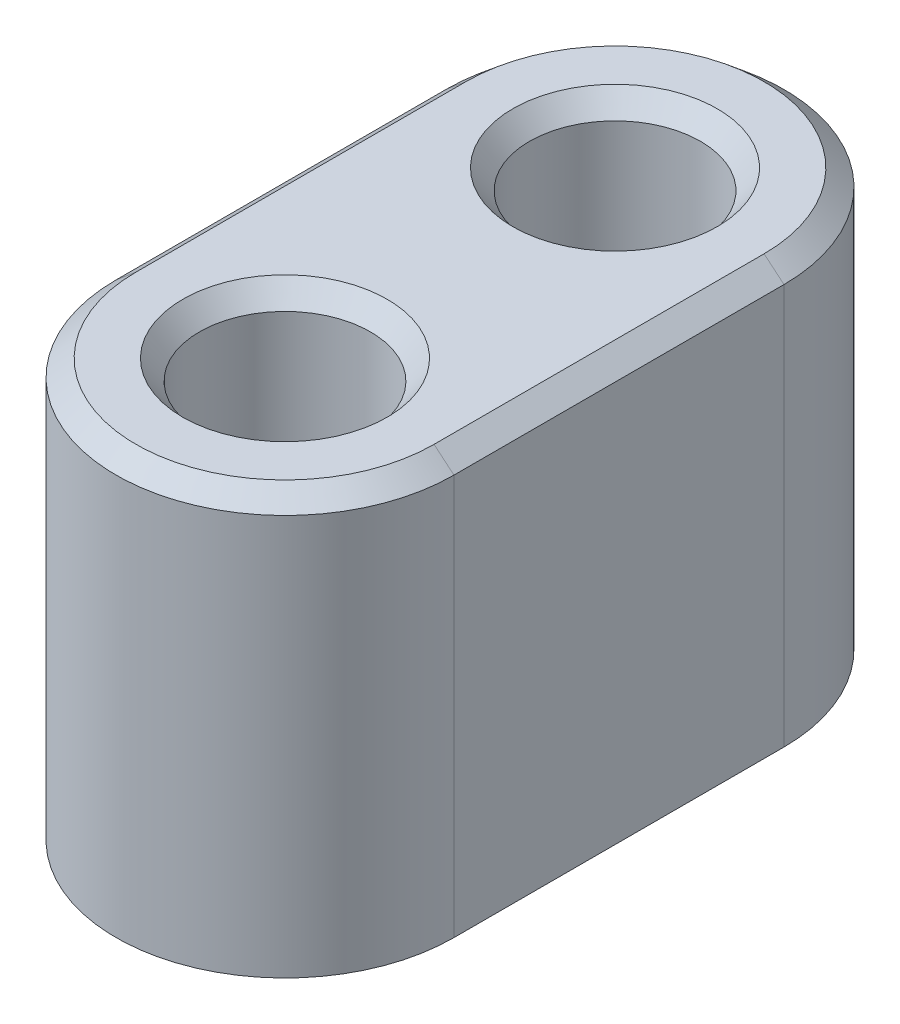
SolidWorks part; units mm, degrees
ref_plane "Front Plane" through (0, 0, 0) normal (0, 0, 1) x (1, 0, 0)
ref_plane "Top Plane" through (0, 0, 0) normal (0, 1, 0) x (1, 0, 0)
ref_plane "Right Plane" through (0, 0, 0) normal (1, 0, 0) x (0, 0, -1)
sketch "Sketch1" plane through (0, 0, 0) normal (0, 1, 0) x (1, 0, 0)
  line L0 (0, -3.955) -> (0, 3.955) construction
  line L1 (-4.05, -3.955) -> (-4.05, 3.955)
  line L2 (4.05, -3.955) -> (4.05, 3.955)
  arc A0 (-4.05, -3.955) -> (4.05, -3.955) centre (0, -3.955) ccw
  arc A1 (4.05, 3.955) -> (-4.05, 3.955) centre (0, 3.955) ccw
  circle A2 centre (0, 3.955) radius 2.05
  circle A3 centre (0, -3.955) radius 2.05
  point P2 (0, 0)
  dimension "D1" = 7.91
  dimension "D2" = 4.1
  dimension "D3" = 2
extrude "Boss-Extrude1" add sketch "Sketch1" along normal blind 10
chamfer "Chamfer1" distance 0.4 angle 50 8 edges at (0, 0, -1.905) (0, 0, 6.005) (4.05, 10, 0) (0, 10, -8.005) (0, 10, 8.005) (-4.05, 10, 0) (0, 10, 6.005) (0, 10, -1.905)
